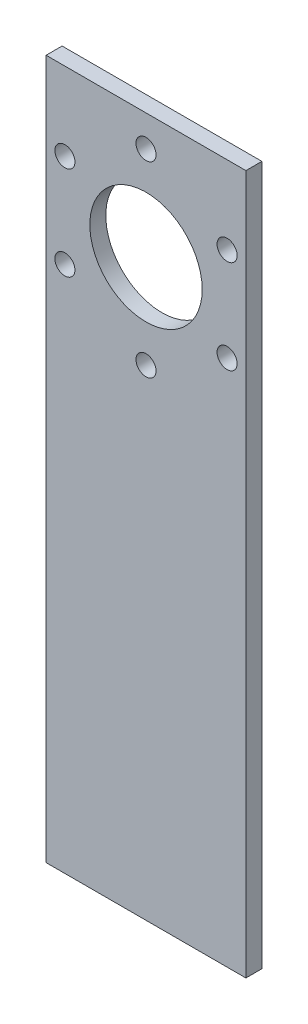
SolidWorks part; units mm, degrees
material "6061-T6 (SS)"
ref_plane "Front Plane" through (0, 0, 0) normal (0, 0, 1) x (1, 0, 0)
ref_plane "Top Plane" through (0, 0, 0) normal (0, 1, 0) x (1, 0, 0)
ref_plane "Right Plane" through (0, 0, 0) normal (1, 0, 0) x (0, 0, -1)
sketch "Sketch2" plane through (0, 0, 0) normal (0, 0, 1) x (1, 0, 0)
  line L0 (25.4, 146.05) -> (25.4, 177.8) construction
  line L1 (0, 0) -> (50.8, 0)
  line L2 (0, 0) -> (0, 177.8)
  line L3 (0, 177.8) -> (50.8, 177.8)
  line L4 (50.8, 0) -> (50.8, 177.8)
  circle A0 centre (25.4, 146.05) radius 14.2875
  dimension "D3" = 28.575
  dimension "D1" = 50.8
  dimension "D2" = 177.8
  dimension "D4" = 31.75
extrude "Boss-Extrude1" add sketch "Sketch2" along normal blind 4.064
hole_wizard "#10 Clearance Hole1" positions "Sketch4" profile "Sketch3" hole size "#10" standard "ANSI Inch" end condition through all
sketch "Sketch4" plane through (0, 0, 4.064) normal (0, 0, 1) x (1, 0, 0)
  line L1 (46.0222, 157.9562) -> (25.4, 169.8625) construction
  line L2 (25.4, 169.8625) -> (4.7778, 157.9563) construction
  line L3 (4.7778, 157.9563) -> (4.7778, 134.1437) construction
  line L4 (4.7778, 134.1437) -> (25.4, 122.2375) construction
  line L5 (25.4, 122.2375) -> (46.0222, 134.1438) construction
  line L6 (46.0222, 134.1438) -> (46.0222, 157.9562) construction
  circle A0 centre (25.4, 146.05) radius 23.8125 construction
  point P2 (46.0222, 157.9562)
  point P3 (25.4, 169.8625)
  point P4 (4.7778, 157.9563)
  point P5 (4.7778, 134.1437)
  point P6 (25.4, 122.2375)
  point P7 (46.0222, 134.1438)
  dimension "D1" = 47.625
sketch "Sketch3" plane through (46.0222, 157.9562, 4.064) normal (1, 0, 0) x (0, -1, 0)
  line L0 (0, 0) -> (0, 4.064)
  line L1 (0, 4.064) -> (2.5527, 4.064)
  line L2 (2.5527, 4.064) -> (2.5527, 0)
  line L5 (2.5527, 0) -> (0, 0)
  line L11 (0, -6.35) -> (0, 107.95) construction
  dimension "Thru Hole Dia." = 5.1054
  dimension "Thru Hole Depth" = 4.064
